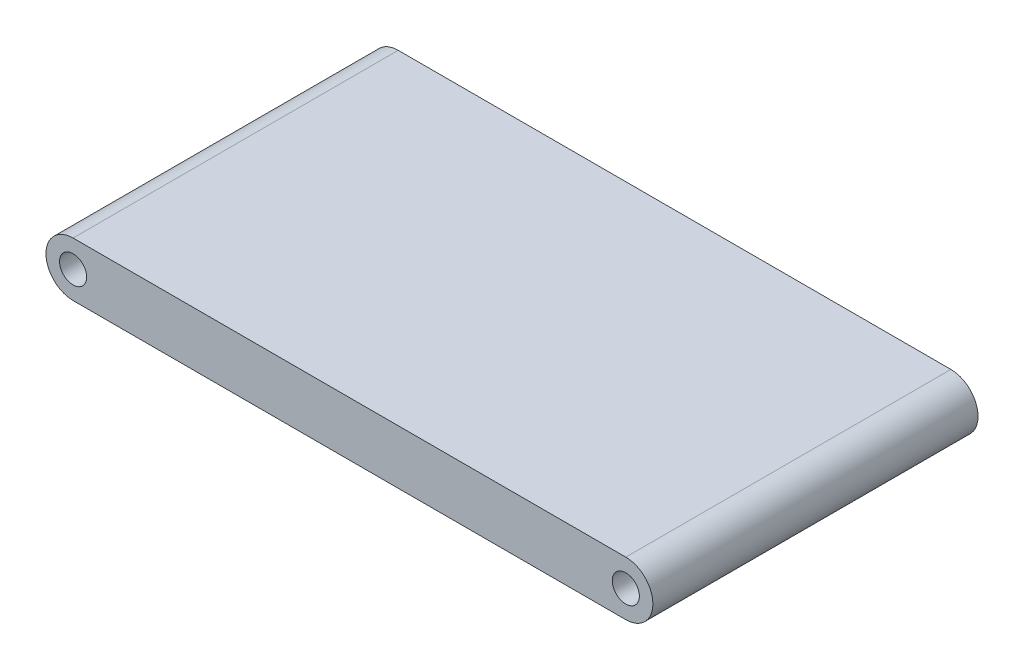
SolidWorks part; units mm, degrees
ref_plane "Front Plane" through (0, 0, 0) normal (0, 0, 1) x (1, 0, 0)
ref_plane "Top Plane" through (0, 0, 0) normal (0, 1, 0) x (1, 0, 0)
ref_plane "Right Plane" through (0, 0, 0) normal (1, 0, 0) x (0, 0, -1)
sketch "Sketch1" plane through (0, 0, 0) normal (0, 0, 1) x (1, 0, 0)
  line L0 (0, 0) -> (129.54, 0) construction
  line L1 (0, 6.35) -> (129.54, 6.35)
  line L2 (0, -6.35) -> (129.54, -6.35)
  circle A0 centre (0, 0) radius 3.175
  circle A1 centre (129.54, 0) radius 3.175
  arc A2 (0, 6.35) -> (0, -6.35) centre (0, 0) ccw
  arc A3 (129.54, 6.35) -> (129.54, -6.35) centre (129.54, 0) cw
  point P11 (0, 0)
  dimension "D4" = 6.35
  dimension "D5" = 6.35
  dimension "D1" = 129.54
  dimension "D3" = 12.7
extrude "Boss-Extrude1" add sketch "Sketch1" along normal blind 76.2
